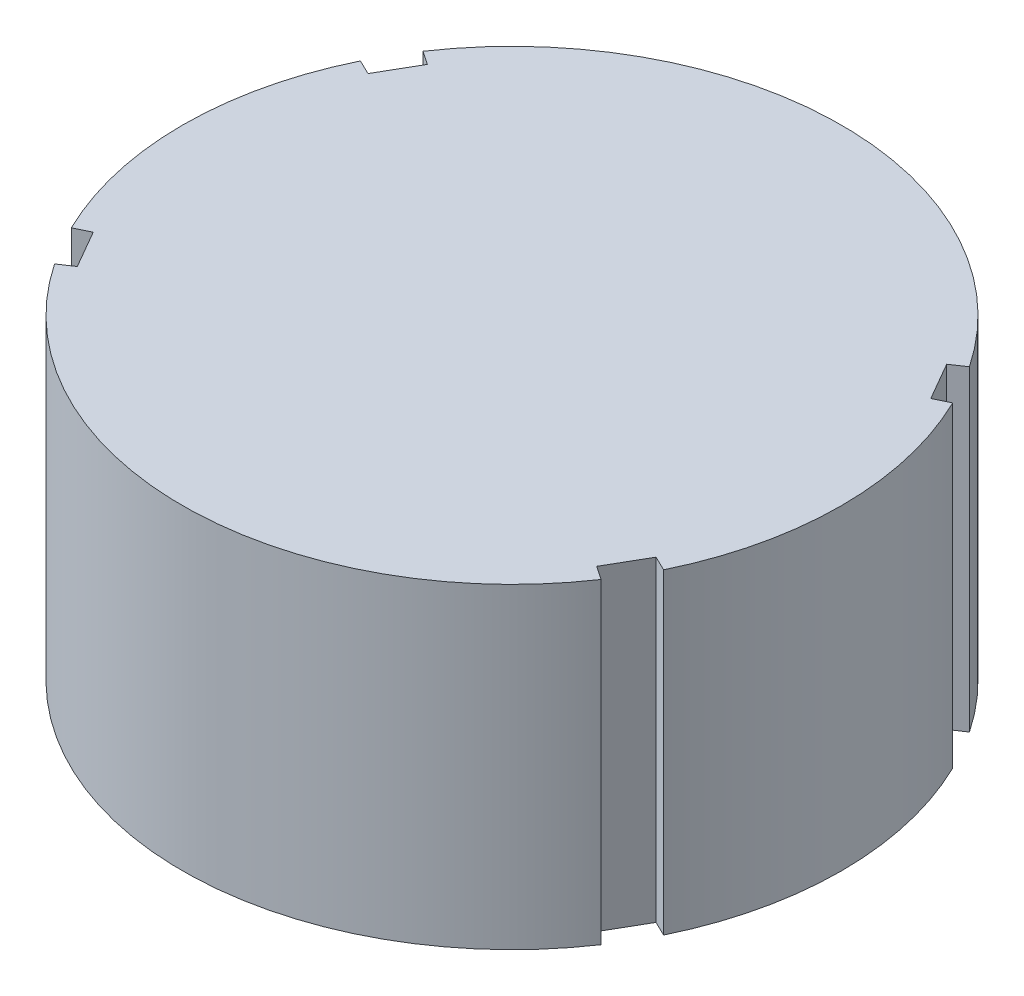
SolidWorks part; units mm, degrees
ref_plane "Front Plane" through (0, 0, 0) normal (0, 0, 1) x (1, 0, 0)
ref_plane "Top Plane" through (0, 0, 0) normal (0, 1, 0) x (1, 0, 0)
ref_plane "Right Plane" through (0, 0, 0) normal (1, 0, 0) x (0, 0, -1)
sketch "Sketch1" plane through (0, 0, 0) normal (0, 1, 0) x (1, 0, 0)
  line L0 (21.6506, 12.5) -> (20.5248, 11.85)
  line L1 (0, 25) -> (-21.6506, 12.5)
  line L2 (-21.6506, 12.5) -> (-21.6506, -12.5)
  line L3 (-21.6506, -12.5) -> (0, -25)
  line L4 (0, -25) -> (21.6506, -12.5)
  line L5 (21.6506, -12.5) -> (21.6506, 12.5)
  line L6 (21.6506, 12.5) -> (0, 25)
  line L7 (19.6998, 13.2789) -> (21.3498, 10.4211)
  line L8 (19.6998, 13.2789) -> (20.7302, 13.9735)
  line L9 (21.3498, 10.4211) -> (22.4665, 10.9661)
  line L10 (19.6998, -13.2789) -> (20.7302, -13.9735)
  line L11 (21.3498, -10.4211) -> (19.6998, -13.2789)
  line L12 (21.3498, -10.4211) -> (22.4665, -10.9661)
  line L13 (21.6506, -12.5) -> (20.5248, -11.85)
  line L14 (-1.65, -23.7) -> (-1.7363, -24.9396) [skipped]
  line L15 (1.65, -23.7) -> (-1.65, -23.7) [skipped]
  line L16 (1.65, -23.7) -> (1.7363, -24.9396) [skipped]
  line L17 (0, -25) -> (0, -23.7) [skipped]
  line L18 (-21.3498, -10.4211) -> (-22.4665, -10.9661)
  line L19 (-19.6998, -13.2789) -> (-21.3498, -10.4211)
  line L20 (-19.6998, -13.2789) -> (-20.7302, -13.9735)
  line L21 (-21.6506, -12.5) -> (-20.5248, -11.85)
  line L22 (-19.6998, 13.2789) -> (-20.7302, 13.9735)
  line L23 (-21.3498, 10.4211) -> (-19.6998, 13.2789)
  line L24 (-21.3498, 10.4211) -> (-22.4665, 10.9661)
  line L25 (-21.6506, 12.5) -> (-20.5248, 11.85)
  circle A0 centre (0, 0) radius 25
  circle A1 centre (0, 0) radius 25 construction
  point P14 (20.5248, 11.85)
  point P43 (0, 0)
  dimension "D1" = 50
  dimension "D2" = 1.3
  dimension "D3" = 3.3
  dimension "D4" = 5
extrude "Boss-Extrude1" add sketch "Sketch1" along normal blind 24 contours L23 L24 L2 L18 L19 L20 L3 L4 L10 L11 L12 L5 L9 L7 L8 L6 L1 L22 | L24 A0 L18 L2 | L1 A0 L22 | L8 A0 L6 | L12 A0 L9 L5 | L4 A0 L10 | L20 A0 L3
